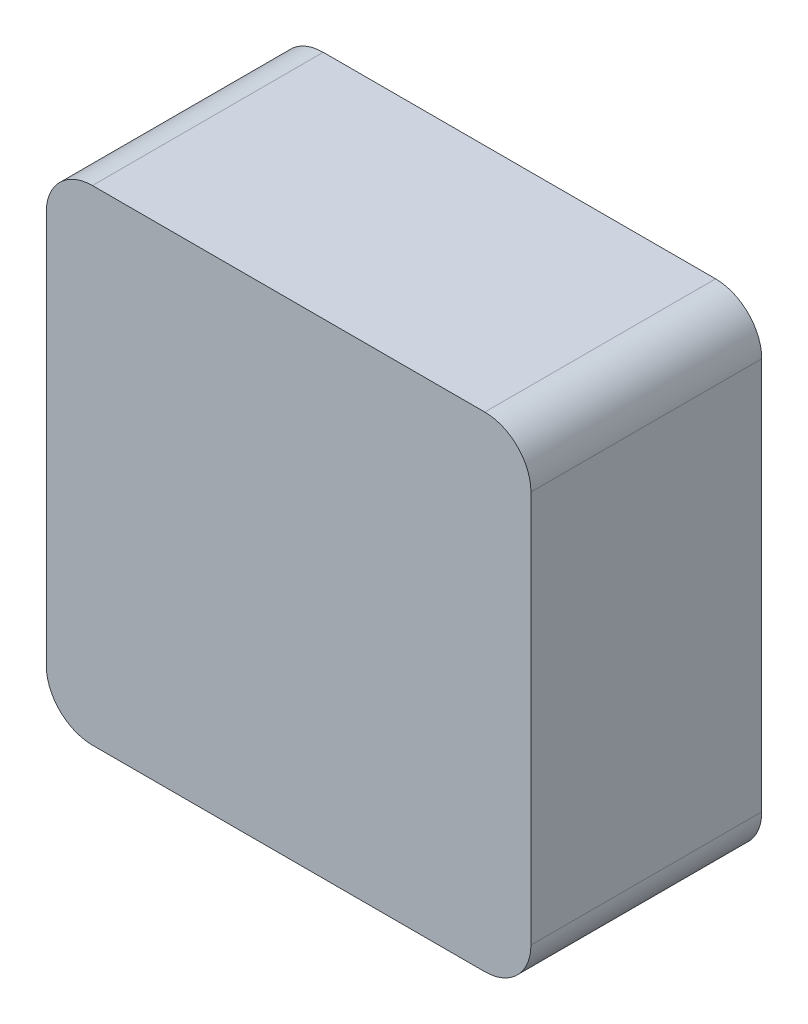
SolidWorks part; units mm, degrees
ref_plane "Front Plane" through (0, 0, 0) normal (0, 0, 1) x (1, 0, 0)
ref_plane "Top Plane" through (0, 0, 0) normal (0, 1, 0) x (1, 0, 0)
ref_plane "Right Plane" through (0, 0, 0) normal (1, 0, 0) x (0, 0, -1)
sketch "Sketch1" plane through (0, 0, 0) normal (0, 1, 0) x (1, 0, 0)
  line L1 (0, 0) -> (53.34, 0)
  line L2 (0, 0) -> (0, 25.4)
  line L3 (0, 25.4) -> (53.34, 25.4)
  line L4 (53.34, 0) -> (53.34, 25.4)
  dimension "D1" = 53.34
  dimension "D2" = 25.4
extrude "Boss-Extrude1" add sketch "Sketch1" along normal blind 53.34
fillet "Fillet1" radius 5.08 4 edges at (53.34, 53.34, -12.7) (0, 53.34, -12.7) (0, 0, -12.7) (53.34, 0, -12.7)
sketch "Sketch2" plane through (0, 0, -25.4) normal (0, 0, -1) x (-1, 0, 0)
  line L0 (-53.34, 48.26) -> (-53.34, 5.08) construction
  line L1 (-46.99, 46.99) -> (-6.35, 46.99)
  line L2 (-46.99, 46.99) -> (-46.99, 6.35)
  line L3 (-46.99, 6.35) -> (-6.35, 6.35)
  line L4 (-6.35, 46.99) -> (-6.35, 6.35)
  line L5 (-48.26, 53.34) -> (-5.08, 53.34) construction
  dimension "D1" = 40.64
  dimension "D2" = 40.64
  dimension "D3" = 6.35
  dimension "D4" = 6.35
extrude "Cut-Extrude1" cut sketch "Sketch2" against normal blind 17.78
fillet "Fillet2" radius 5.08 4 edges at (6.35, 6.35, -16.51) (46.99, 6.35, -16.51) (46.99, 46.99, -16.51) (6.35, 46.99, -16.51)
